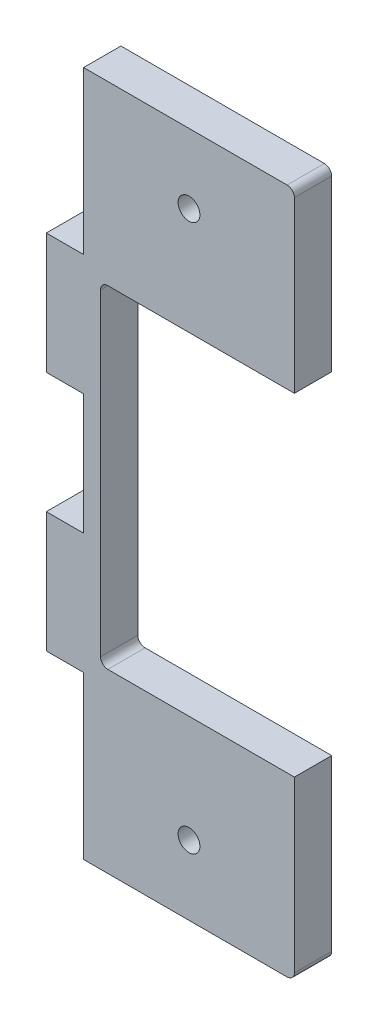
SolidWorks part; units mm, degrees
ref_plane "Front Plane" through (0, 0, 0) normal (0, 0, 1) x (1, 0, 0)
ref_plane "Top Plane" through (0, 0, 0) normal (0, 1, 0) x (1, 0, 0)
ref_plane "Right Plane" through (0, 0, 0) normal (1, 0, 0) x (0, 0, -1)
sketch "Sketch1" plane through (0, 0, 0) normal (0, 0, 1) x (1, 0, 0)
  line L0 (-16.4709, 7.1631) -> (-16.4709, -9.4369)
  line L13 (-16.4709, -48.3169) -> (11.5291, -48.3169)
  line L14 (-16.4709, 46.0431) -> (11.5291, 46.0431)
  line L15 (-16.4709, -9.4369) -> (-21.6009, -9.4369)
  line L16 (-16.4709, 7.1631) -> (-21.6009, 7.1631)
  line L65 (12.5291, -47.3169) -> (12.5291, 45.0431)
  line L66 (-21.6009, -9.4369) -> (-21.6009, -26.0369)
  line L67 (-21.6009, 7.1631) -> (-21.6009, 23.7631)
  line L68 (-21.6009, -26.0369) -> (-16.4709, -26.0369)
  line L69 (-16.4709, -26.0369) -> (-16.4709, -48.3169)
  line L70 (-21.6009, 23.7631) -> (-16.4709, 23.7631)
  line L71 (-16.4709, 23.7631) -> (-16.4709, 46.0431)
  circle A0 centre (-1.9709, -38.7509) radius 1.5
  circle A1 centre (-1.9709, 36.4771) radius 1.5
  arc A2 (12.5291, 45.0431) -> (11.5291, 46.0431) centre (11.5291, 45.0431) ccw
  arc A3 (11.5291, -48.3169) -> (12.5291, -47.3169) centre (11.5291, -47.3169) ccw
  point P24 (12.5291, 46.0431)
  point P27 (12.5291, -48.3169)
  dimension "D5" = 3
  dimension "D6" = 3
  dimension "D17" = 1
  dimension "D18" = 1
  dimension "D4" = 5.13
  dimension "D7" = 29
  dimension "D8" = 5.13
  dimension "D9" = 16.6
  dimension "D10" = 16.6
  dimension "D11" = 22.28
  dimension "D12" = 22.28
  dimension "D13" = 14.5
  dimension "D14" = 14.5
  dimension "D15" = 9.566
  dimension "D16" = 9.566
  dimension "D20" = 94.36
  dimension "D24" = 29
extrude "Boss-Extrude1" add sketch "Sketch1" along normal blind 5.13
sketch "Sketch2" plane through (0, 0, 5.13) normal (0, 0, 1) x (1, 0, 0)
  line L0 (12.5291, -47.3169) -> (12.5291, 45.0431) construction
  line L1 (12.5291, 21.7231) -> (-13.1409, 21.7231)
  line L2 (12.5291, 21.7231) -> (12.5291, -23.9969)
  line L3 (12.5291, -23.9969) -> (-13.1409, -23.9969)
  line L4 (-14.1409, 20.7231) -> (-14.1409, -22.9969)
  line L5 (11.5291, 46.0431) -> (-16.4709, 46.0431) construction
  arc A0 (-13.1409, -23.9969) -> (-14.1409, -22.9969) centre (-13.1409, -22.9969) cw
  arc A1 (-14.1409, 20.7231) -> (-13.1409, 21.7231) centre (-13.1409, 20.7231) cw
  point P10 (-14.1409, -23.9969)
  point P13 (-14.1409, 21.7231)
  dimension "D4" = 1
  dimension "D1" = 45.72
  dimension "D2" = 26.67
  dimension "D3" = 24.32
extrude "Cut-Extrude1" cut sketch "Sketch2" against normal up to next
equation "\"D13@Sketch1\" = \"D7@Sketch1\"/2"
equation "\"D14@Sketch1\" = \"D13@Sketch1\""
equation "\"D3@Sketch2\" = (\"D20@Sketch1\"-\"D1@Sketch2\")/2"
